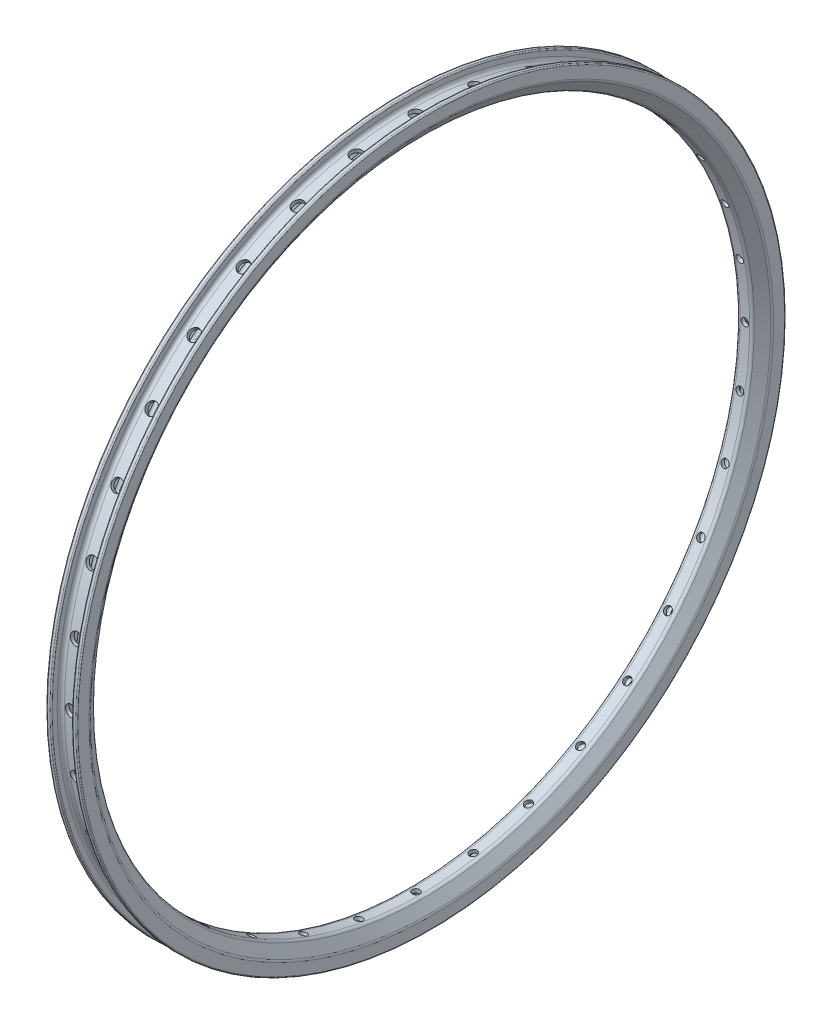
SolidWorks part; units mm, degrees
ref_plane "Front Plane" through (0, 0, 0) normal (0, 0, 1) x (1, 0, 0)
ref_plane "Top Plane" through (0, 0, 0) normal (0, 1, 0) x (1, 0, 0)
ref_plane "Right Plane" through (0, 0, 0) normal (1, 0, 0) x (0, 0, -1)
sketch "Sketch1" plane through (0, 0, 0) normal (0, 0, 1) x (1, 0, 0)
  line L0 (-16.1754, 0) -> (21.945, 0)
  line L1 (2.8848, 0) -> (0, 0)
sketch "Sketch2" plane through (0, 0, 0) normal (0, 0, 1) x (1, 0, 0)
  line L0 (0, 0) -> (0, 290)
  dimension "D1" = 290
sketch "Sketch3" plane through (0, 0, 0) normal (0, 0, 1) x (1, 0, 0)
  line L0 (0, 269) -> (0, 290) construction
  line L1 (-3.938, 269) -> (3.938, 269)
  line L2 (0, 0) -> (0, 290) construction
  line L3 (0, 290) -> (-12.5, 290) construction
  line L4 (-12.5, 289) -> (-12.5, 279.9457)
  line L5 (-11.5, 290) -> (-9.5, 290)
  line L6 (-8.5, 289) -> (-8.5, 285)
  line L7 (-5.5, 282) -> (5.5, 282)
  line L8 (8.5, 285) -> (8.5, 289)
  line L9 (9.5, 290) -> (11.5, 290)
  line L10 (12.5, 289) -> (12.5, 279.9457)
  line L11 (-11.9577, 278.2253) -> (-6.3957, 270.2796)
  line L12 (11.9577, 278.2253) -> (6.3957, 270.2796)
  line L13 (-4.538, 272) -> (4.538, 272)
  line L17 (11, 279.9457) -> (11, 287.6)
  line L19 (10.4577, 278.2253) -> (6.9957, 273.2796)
  line L23 (-10.4577, 278.2253) -> (-6.9957, 273.2796)
  line L25 (10.6, 288) -> (10.4, 288)
  line L26 (10, 287.6) -> (10, 282)
  line L27 (7, 279) -> (-7, 279)
  line L28 (-10, 282) -> (-10, 287.6)
  line L29 (-10.4, 288) -> (-10.6, 288)
  line L30 (-11, 287.6) -> (-11, 279.9457)
  arc A0 (-8.5, 285) -> (-5.5, 282) centre (-5.5, 285) ccw
  arc A1 (5.5, 282) -> (8.5, 285) centre (5.5, 285) ccw
  arc A2 (3.938, 269) -> (6.3957, 270.2796) centre (3.938, 272) ccw
  arc A3 (-3.938, 269) -> (-6.3957, 270.2796) centre (-3.938, 272) cw
  arc A4 (-12.5, 279.9457) -> (-11.9577, 278.2253) centre (-9.5, 279.9457) ccw
  arc A5 (12.5, 279.9457) -> (11.9577, 278.2253) centre (9.5, 279.9457) cw
  arc A6 (11.5, 290) -> (12.5, 289) centre (11.5, 289) cw
  arc A7 (8.5, 289) -> (9.5, 290) centre (9.5, 289) cw
  arc A8 (-9.5, 290) -> (-8.5, 289) centre (-9.5, 289) cw
  arc A9 (-11.5, 290) -> (-12.5, 289) centre (-11.5, 289) ccw
  arc A10 (11, 279.9457) -> (10.4577, 278.2253) centre (8, 279.9457) cw
  arc A11 (-11, 279.9457) -> (-10.4577, 278.2253) centre (-8, 279.9457) ccw
  arc A12 (-4.538, 272) -> (-6.9957, 273.2796) centre (-4.538, 275) cw
  arc A13 (4.538, 272) -> (6.9957, 273.2796) centre (4.538, 275) ccw
  arc A14 (10, 282) -> (7, 279) centre (7, 282) cw
  arc A15 (-7, 279) -> (-10, 282) centre (-7, 282) cw
  arc A16 (11, 287.6) -> (10.6, 288) centre (10.6, 287.6) ccw
  arc A17 (-10, 287.6) -> (-10.4, 288) centre (-10.4, 287.6) ccw
  arc A18 (10.4, 288) -> (10, 287.6) centre (10.4, 287.6) ccw
  arc A19 (-10.6, 288) -> (-11, 287.6) centre (-10.6, 287.6) ccw
  point P0 (0, 70.4672)
  point P1 (0, 269)
  point P12 (0, 71.1174)
  point P23 (5.5, 269)
  point P26 (-5.5, 269)
  point P38 (-8.5, 290)
  point P47 (0, 279.9457)
  point P56 (-11, 279)
  point P74 (10.5, 290)
  dimension "D1" = 269
  dimension "D2" = 11
  dimension "D3" = 3
  dimension "D4" = 1
  dimension "D10" = 3
  dimension "D11" = 0.4
  dimension "D5" = 1.5
  dimension "D6" = 1.5
  dimension "D7" = 3
  dimension "D8" = 1.5
  dimension "D9" = 3
  dimension "D12" = 8
revolve "Revolve1" add sketch "Sketch3" angle 180 about L0
ref_plane "Plane1" through (0, 290, 0) normal (0, 1, 0) x (-1, 0, 0)
sketch "Holes spokes" plane through (0, 290, 0) normal (0, 1, 0) x (-1, 0, 0)
  circle A0 centre (0, 0) radius 3.1
  dimension "D1" = 6.2
extrude "Cut-Extrude1" cut sketch "Holes spokes" against normal blind 26
pattern_circular "Круговой массив1" count 36 over 360 about axis through (-16.1754, 0, 0) along (-1, 0, 0) of "Cut-Extrude1"
sketch "Эскиз1" plane through (0, 0, 0) normal (1, 0, 0) x (0, 0, -1)
  line L0 (0, 290) -> (0, 269)
  line L1 (50.358, 285.5942) -> (46.7114, 264.9133)
  line L2 (99.1858, 272.5109) -> (92.0034, 252.7773)
  line L3 (145, 251.1474) -> (134.5, 232.9608)
  line L4 (186.4084, 222.1529) -> (172.9099, 206.066)
  line L5 (222.1529, 186.4084) -> (206.066, 172.9099)
  line L6 (251.1474, 145) -> (232.9608, 134.5)
  line L7 (272.5109, 99.1858) -> (252.7773, 92.0034)
  line L8 (285.5942, 50.358) -> (264.9133, 46.7114)
  line L9 (290, 0) -> (269, 0)
  line L10 (285.5942, -50.358) -> (264.9133, -46.7114)
  line L11 (272.5109, -99.1858) -> (252.7773, -92.0034)
  line L12 (251.1474, -145) -> (232.9608, -134.5)
  line L13 (222.1529, -186.4084) -> (206.066, -172.9099)
  line L14 (186.4084, -222.1529) -> (172.9099, -206.066)
  line L15 (145, -251.1474) -> (134.5, -232.9608)
  line L16 (99.1858, -272.5109) -> (92.0034, -252.7773)
  line L17 (50.358, -285.5942) -> (46.7114, -264.9133)
  line L18 (0, -290) -> (0, -269)
  line L19 (-50.358, -285.5942) -> (-46.7114, -264.9133)
  line L20 (-99.1858, -272.5109) -> (-92.0034, -252.7773)
  line L21 (-145, -251.1474) -> (-134.5, -232.9608)
  line L22 (-186.4084, -222.1529) -> (-172.9099, -206.066)
  line L23 (-222.1529, -186.4084) -> (-206.066, -172.9099)
  line L24 (-251.1474, -145) -> (-232.9608, -134.5)
  line L25 (-272.5109, -99.1858) -> (-252.7773, -92.0034)
  line L26 (-285.5942, -50.358) -> (-264.9133, -46.7114)
  line L27 (-290, 0) -> (-269, 0)
  line L28 (-285.5942, 50.358) -> (-264.9133, 46.7114)
  line L29 (-272.5109, 99.1858) -> (-252.7773, 92.0034)
  line L30 (-251.1474, 145) -> (-232.9608, 134.5)
  line L31 (-222.1529, 186.4084) -> (-206.066, 172.9099)
  line L32 (-186.4084, 222.1529) -> (-172.9099, 206.066)
  line L33 (-145, 251.1474) -> (-134.5, 232.9608)
  line L34 (-99.1858, 272.5109) -> (-92.0034, 252.7773)
  line L35 (-50.358, 285.5942) -> (-46.7114, 264.9133)
  point P77 (0, 0)
  dimension "D1" = 21
  dimension "D2" = 36
sketch "Эскиз2" plane through (0, 290, 0) normal (0, 1, 0) x (-1, 0, 0)
  circle A0 centre (0, 0) radius 4.75
extrude "Вырез-Вытянуть1" cut sketch "Эскиз2" against normal blind 12
pattern_circular "Круговой массив2" count 36 every 10 about axis through (-16.1754, 0, 0) along (-1, 0, 0) of "Вырез-Вытянуть1"
